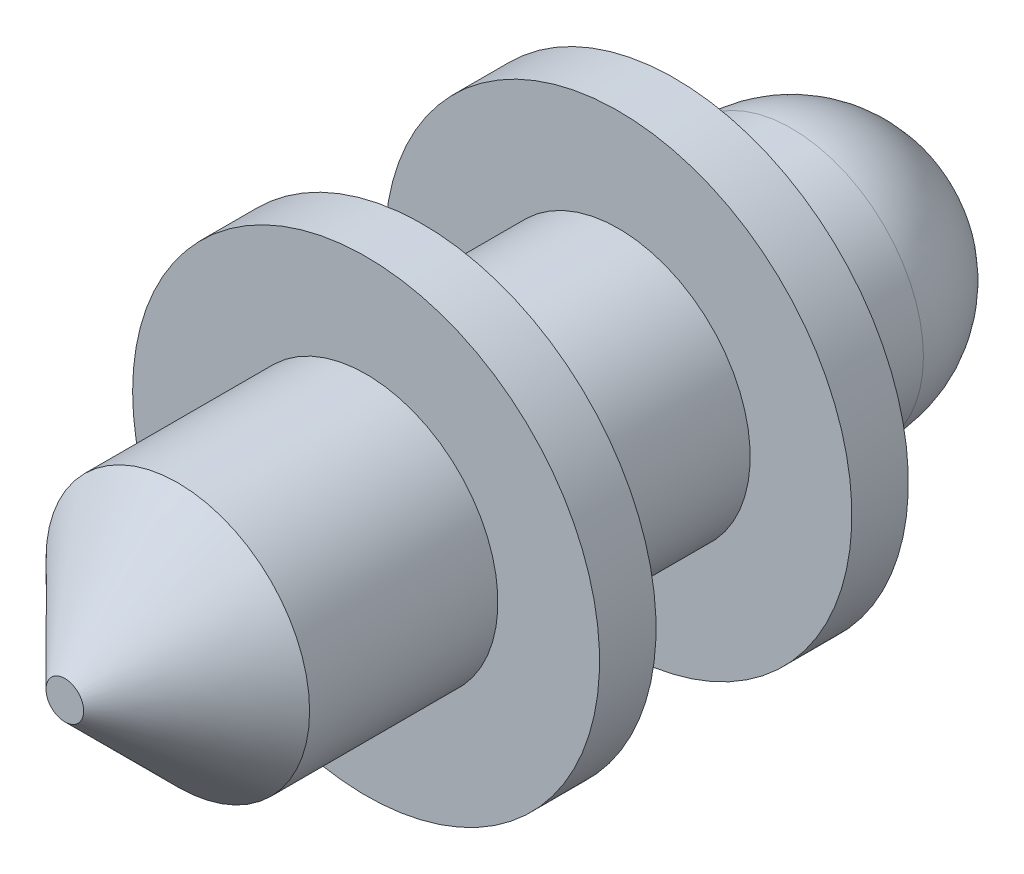
SolidWorks part; units mm, degrees
ref_plane "Plan de face" through (0, 0, 0) normal (0, 0, 1) x (1, 0, 0)
ref_plane "Plan de dessus" through (0, 0, 0) normal (0, 1, 0) x (1, 0, 0)
ref_plane "Plan de droite" through (0, 0, 0) normal (1, 0, 0) x (0, 0, -1)
sketch "Esquisse1" plane through (0, 0, 0) normal (0, 0, 1) x (1, 0, 0)
  circle A0 centre (0, 0) radius 1.75
extrude "Boss.-Extru.1" add sketch "Esquisse1" along normal blind 4
sketch "Esquisse3" plane through (0, 0, 0) normal (0, 0, -1) x (-1, 0, 0)
  circle A0 centre (0, 0) radius 3.1
extrude "Boss.-Extru.2" add sketch "Esquisse3" along normal blind 0.75
sketch "Esquisse4" plane through (0, 0, -0.75) normal (0, 0, -1) x (-1, 0, 0)
  circle A0 centre (0, 0) radius 1.75
extrude "Boss.-Extru.3" add sketch "Esquisse4" along normal blind 2.6
sketch "Esquisse5" plane through (0, 0, -3.35) normal (0, 0, -1) x (-1, 0, 0)
  circle A0 centre (0, 0) radius 3.1
extrude "Boss.-Extru.4" add sketch "Esquisse5" along normal blind 0.75
sketch "Esquisse6" plane through (0, 0, -4.1) normal (0, 0, -1) x (-1, 0, 0)
  circle A0 centre (0, 0) radius 1.75
extrude "Boss.-Extru.5" add sketch "Esquisse6" along normal blind 3.3
chamfer "Chanfrein1" distance 1.5 angle 45 1 edges at (1.75, 0, 4)
fillet "Congé1" radius 1.75 1 edges at (-1.75, 0, -7.4)
